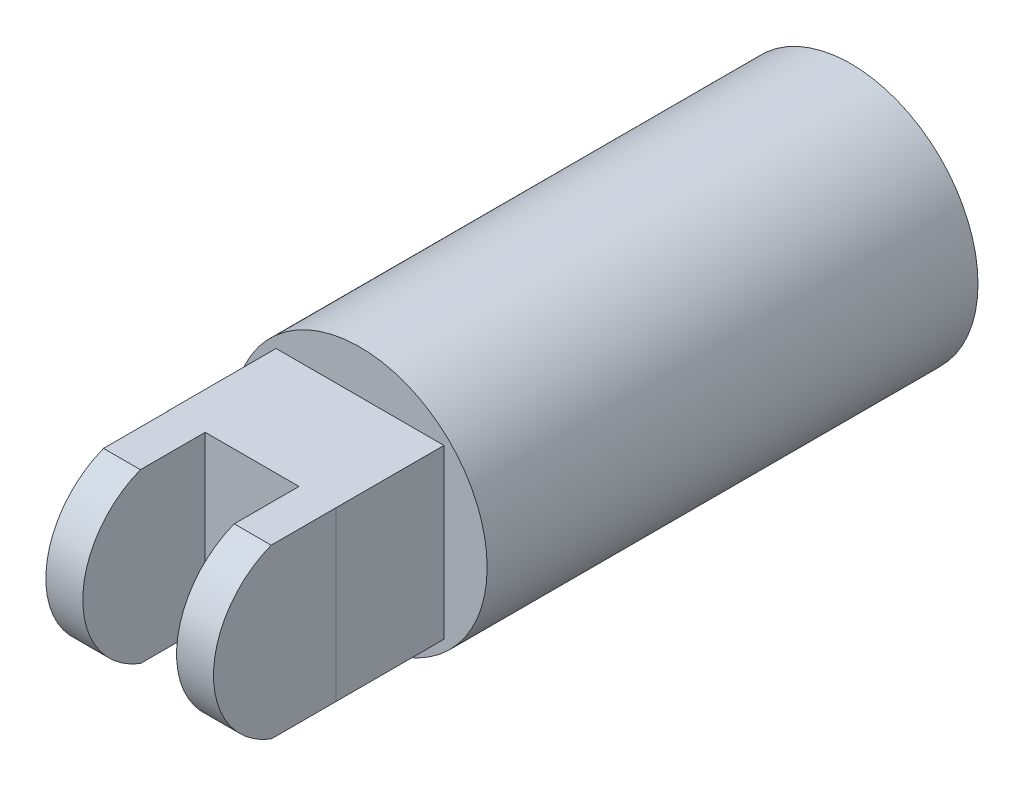
SolidWorks part; units mm, degrees
ref_plane "Front Plane" through (0, 0, 0) normal (0, 0, 1) x (1, 0, 0)
ref_plane "Top Plane" through (0, 0, 0) normal (0, 1, 0) x (1, 0, 0)
ref_plane "Right Plane" through (0, 0, 0) normal (1, 0, 0) x (0, 0, -1)
sketch "Sketch1" plane through (0, 0, 0) normal (0, 0, 1) x (1, 0, 0)
  circle A0 centre (0, 0) radius 6.475
  dimension "D1" = 12.95
extrude "Boss-Extrude1" add sketch "Sketch1" along normal blind 25
sketch "Sketch5" plane through (0, 0, 25) normal (0, 0, 1) x (1, 0, 0)
  line L1 (4.275, -4.275) -> (-4.275, -4.275)
  line L2 (4.275, -4.275) -> (4.275, 4.275)
  line L3 (4.275, 4.275) -> (-4.275, 4.275)
  line L4 (-4.275, -4.275) -> (-4.275, 4.275)
  line L5 (4.275, -4.275) -> (-4.275, 4.275) construction
  line L6 (4.275, 4.275) -> (-4.275, -4.275) construction
  point P0 (0, 0)
  dimension "D1" = 8.55
  dimension "D2" = 8.55
extrude "Boss-Extrude2" add sketch "Sketch5" along normal blind 5.5
sketch "Sketch8" plane through (0, 0, 30.5) normal (0, 0, 1) x (1, 0, 0)
  line L0 (4.275, 4.275) -> (-4.275, 4.275) construction
  line L1 (4.275, -4.275) -> (2.395, -4.275)
  line L2 (4.275, -4.275) -> (4.275, 4.275)
  line L3 (4.275, 4.275) -> (2.395, 4.275)
  line L4 (2.395, -4.275) -> (2.395, 4.275)
  line L5 (4.275, -4.275) -> (2.395, 4.275) construction
  line L6 (4.275, 4.275) -> (2.395, -4.275) construction
  point P0 (3.335, 0)
  dimension "D1" = 1.88
sketch "Sketch10" plane through (0, 0, 30.5) normal (0, 0, 1) x (1, 0, 0)
  line L1 (-2.3829, -4.275) -> (-4.2629, -4.275)
  line L2 (-2.3829, -4.275) -> (-2.3829, 4.275)
  line L3 (-2.3829, 4.275) -> (-4.2629, 4.275)
  line L4 (-4.2629, -4.275) -> (-4.2629, 4.275)
  line L5 (-2.3829, -4.275) -> (-4.2629, 4.275) construction
  line L6 (-2.3829, 4.275) -> (-4.2629, -4.275) construction
  point P0 (-3.3229, 0)
  dimension "D1" = 1.88
extrude "Boss-Extrude3" add sketch "Sketch10" along normal blind 3.3
extrude "Boss-Extrude4" add sketch "Sketch8" along normal blind 3.3
sketch "Sketch11" plane through (4.275, 0, 0) normal (1, 0, 0) x (0, 0, -1)
  line L0 (-33.8, 4.275) -> (-33.8, -4.275)
  arc A0 (-33.8, 4.275) -> (-33.8, -4.275) centre (-32.1566, 0) ccw
  dimension "D1" = 4.58
sketch "Sketch12" plane through (-4.2629, 0, 0) normal (-1, 0, 0) x (0, 0, 1)
  line L0 (33.8, 4.275) -> (33.8, -4.275)
  arc A0 (33.8, 4.275) -> (33.8, -4.275) centre (32.1566, 0) cw
extrude "Boss-Extrude5" add sketch "Sketch11" against normal blind 1.88
extrude "Boss-Extrude6" add sketch "Sketch12" against normal blind 1.88
